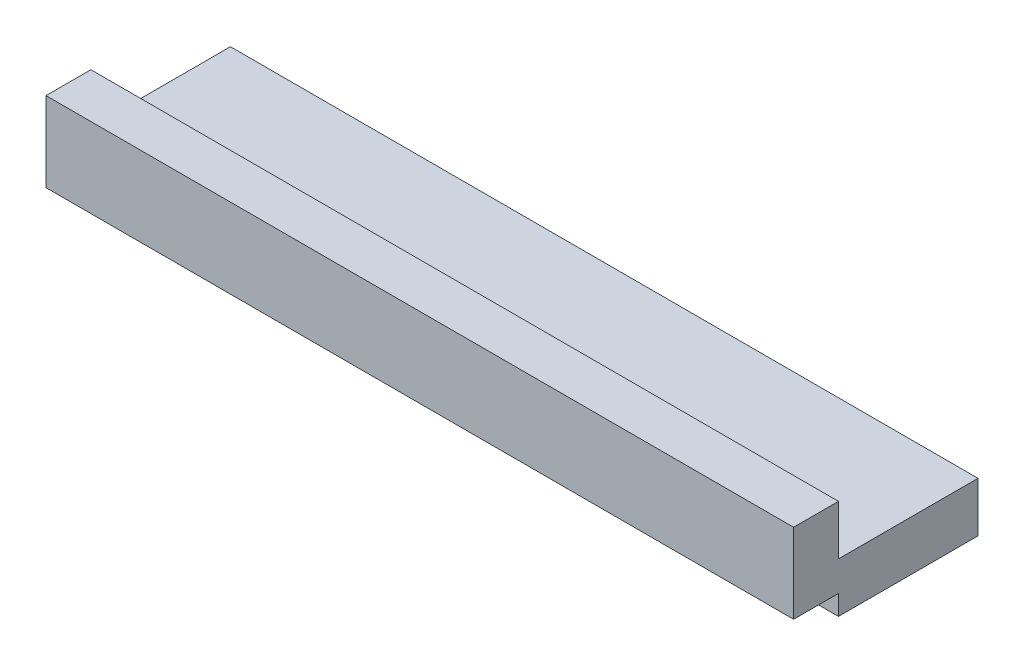
SolidWorks part; units mm, degrees
ref_plane "Front Plane" through (0, 0, 0) normal (0, 0, 1) x (1, 0, 0)
ref_plane "Top Plane" through (0, 0, 0) normal (0, 1, 0) x (1, 0, 0)
ref_plane "Right Plane" through (0, 0, 0) normal (1, 0, 0) x (0, 0, -1)
sketch "Sketch1" plane through (0, 0, 0) normal (0, 1, 0) x (1, 0, 0)
  line L1 (-27.7861, 0.4079) -> (10.3139, 0.4079)
  line L2 (-27.7861, 0.4079) -> (-27.7861, 2.6939)
  line L3 (-27.7861, 2.6939) -> (10.3139, 2.6939)
  line L4 (10.3139, 0.4079) -> (10.3139, 2.6939)
  dimension "D1" = 2.286
  dimension "D2" = 38.1
extrude "Boss-Extrude1" add sketch "Sketch1" along normal blind 4.064
sketch "Sketch2" [suppressed] plane through (0, 4.064, 0) normal (0, 1, 0) x (1, 0, 0)
  line L0 (-18.8961, 2.6939) -> (-18.8961, 0.4079) construction
  line L1 (10.3139, 0.4079) -> (-18.8961, 0.4079)
  line L2 (10.3139, 0.4079) -> (10.3139, 2.6939)
  line L3 (10.3139, 2.6939) -> (-18.8961, 2.6939)
  line L4 (-18.8961, 0.4079) -> (-18.8961, 2.6939)
  point P8 (-18.8961, 1.5509)
sketch "Sketch3" plane through (0, 0, -2.6939) normal (0, 0, -1) x (-1, 0, 0)
  line L0 (-10.3139, 4.064) -> (-10.3139, 0) construction
  line L1 (27.7861, 1.524) -> (-10.3139, 1.524)
  line L2 (27.7861, 1.524) -> (27.7861, -1.016)
  line L3 (27.7861, -1.016) -> (-10.3139, -1.016)
  line L4 (-10.3139, 1.524) -> (-10.3139, -1.016)
  line L5 (27.7861, 4.064) -> (27.7861, 0) construction
  line L6 (-10.3139, 0) -> (27.7861, 0) construction
  point P9 (27.7861, 2.032)
  dimension "D1" = 2.54
  dimension "D2" = 1.524
extrude "Boss-Extrude3" add sketch "Sketch3" along normal blind 7.112
sketch "Sketch4" plane through (-27.7861, 0, 0) normal (-1, 0, 0) x (0, 0, 1)
  line L1 (-2.6939, -1.016) -> (-3.4559, -1.016)
  line L2 (-2.6939, -1.016) -> (-2.6939, 0)
  line L3 (-2.6939, 0) -> (-3.4559, 0)
  line L4 (-3.4559, -1.016) -> (-3.4559, 0)
  dimension "D1" = 0.762
extrude "Cut-Extrude1" cut sketch "Sketch4" against normal blind 30.734
